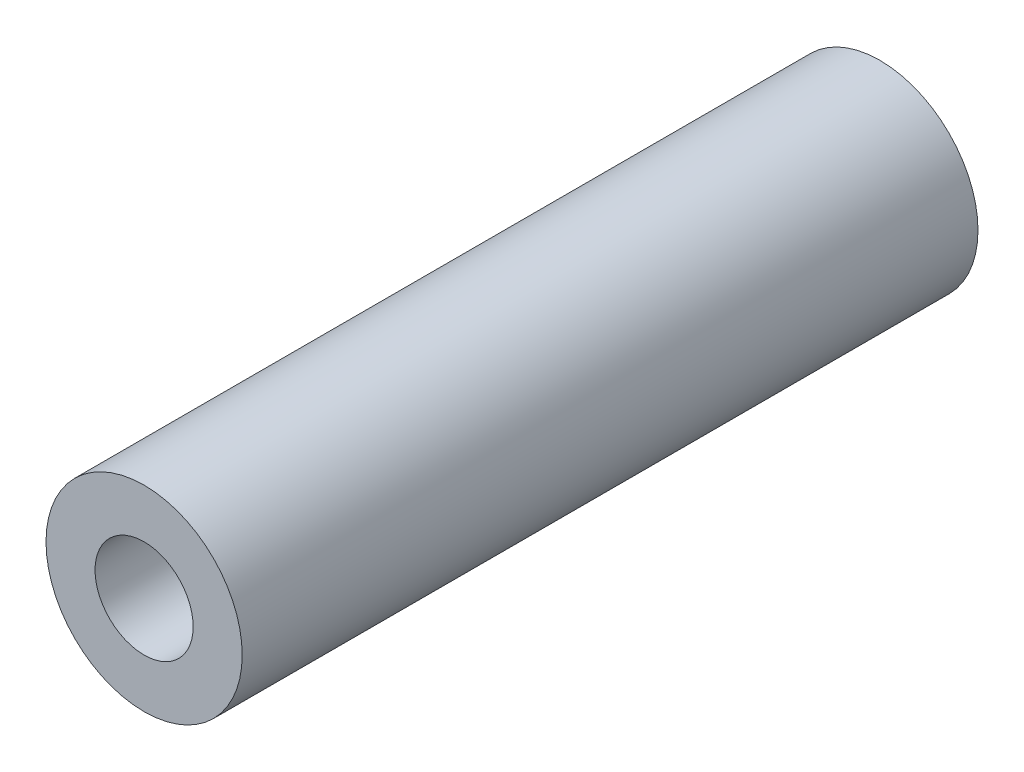
SolidWorks part; units mm, degrees
ref_plane "Front Plane" through (0, 0, 0) normal (0, 0, 1) x (1, 0, 0)
ref_plane "Top Plane" through (0, 0, 0) normal (0, 1, 0) x (1, 0, 0)
ref_plane "Right Plane" through (0, 0, 0) normal (1, 0, 0) x (0, 0, -1)
sketch "Sketch1" plane through (0, 0, 0) normal (0, 0, 1) x (1, 0, 0)
  circle A0 centre (0, 0) radius 2
  circle A1 centre (0, 0) radius 4
  dimension "D1" = 4
  dimension "D2" = 8
extrude "Boss-Extrude1" add sketch "Sketch1" along normal blind 30
